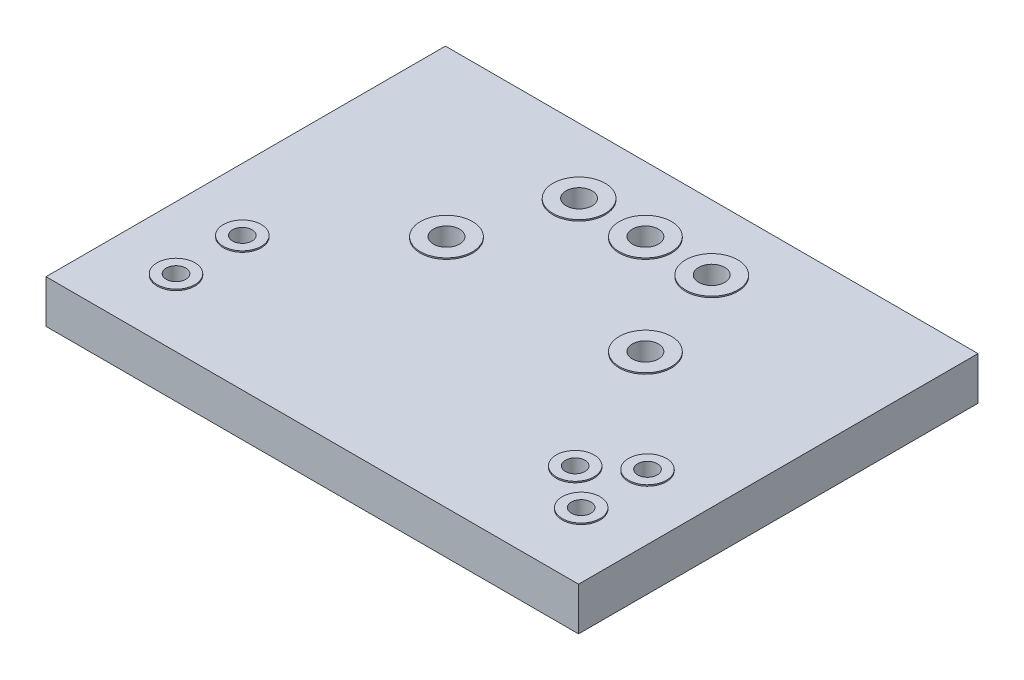
SolidWorks part; units mm, degrees
ref_plane "Front Plane" through (0, 0, 0) normal (0, 0, 1) x (1, 0, 0)
ref_plane "Top Plane" through (0, 0, 0) normal (0, 1, 0) x (1, 0, 0)
ref_plane "Right Plane" through (0, 0, 0) normal (1, 0, 0) x (0, 0, -1)
sketch "Sketch3" plane through (0, 0, 0) normal (0, 1, 0) x (1, 0, 0)
  line L0 (7.76, -2.57) -> (7.76, -5.11) construction
  line L1 (-10.2, 7.65) -> (10.2, 7.65)
  line L2 (-10.2, 7.65) -> (-10.2, -7.65)
  line L3 (-10.2, -7.65) -> (10.2, -7.65)
  line L4 (10.2, 7.65) -> (10.2, -7.65)
  line L5 (-10.2, 7.65) -> (10.2, -7.65) construction
  line L6 (-10.2, -7.65) -> (10.2, 7.65) construction
  line L7 (6.26, -3.84) -> (7.76, -3.84) construction
  line L8 (-7.76, -2.57) -> (-7.76, -5.11) construction
  line L9 (-7.76, -3.84) -> (7.76, -3.84) construction
  line L10 (-2.54, 5.11) -> (2.54, 5.11) construction
  line L11 (-3.81, 1.3) -> (3.81, 1.3) construction
  circle A0 centre (-2.54, 5.11) radius 0.5
  circle A1 centre (0, 5.11) radius 0.5
  circle A2 centre (2.54, 5.11) radius 0.5
  circle A3 centre (-7.76, -2.57) radius 0.375
  circle A4 centre (-7.76, -5.11) radius 0.375
  circle A5 centre (7.76, -2.57) radius 0.375
  circle A6 centre (7.76, -5.11) radius 0.375
  circle A7 centre (6.26, -3.84) radius 0.375
  circle A8 centre (-3.81, 1.3) radius 0.5
  circle A9 centre (3.81, 1.3) radius 0.5
  point P0 (0, 0)
  point P24 (0, -3.84)
  point P28 (0, 1.3)
  dimension "D5" = 0.75
  dimension "D7" = 1
  dimension "D1" = 15.3
  dimension "D2" = 20.4
  dimension "D3" = 1.5
  dimension "D4" = 2.54
  dimension "D6" = 15.52
  dimension "D8" = 2.54
  dimension "D9" = 2.54
  dimension "D10" = 2.54
  dimension "D11" = 7.62
  dimension "D12" = 3.81
extrude "Boss-Extrude2" add sketch "Sketch3" along normal mid plane 1.65
sketch "Sketch5" plane through (0, 0.825, 0) normal (0, 1, 0) x (1, 0, 0)
  circle A4 centre (7.76, -5.11) radius 0.375 construction
  circle A5 centre (6.26, -3.84) radius 0.375 construction
  circle A6 centre (7.76, -2.57) radius 0.375 construction
  circle A7 centre (-7.76, -5.11) radius 0.375 construction
  circle A8 centre (-7.76, -2.57) radius 0.375 construction
  circle A9 centre (-3.81, 1.3) radius 0.5 construction
  circle A10 centre (3.81, 1.3) radius 0.5 construction
  circle A11 centre (2.54, 5.11) radius 0.5 construction
  circle A12 centre (0, 5.11) radius 0.5 construction
  circle A13 centre (-2.54, 5.11) radius 0.5 construction
  circle A14 centre (7.76, -5.11) radius 0.375
  circle A15 centre (6.26, -3.84) radius 0.375
  circle A16 centre (7.76, -2.57) radius 0.375
  circle A17 centre (-7.76, -5.11) radius 0.375
  circle A18 centre (-7.76, -2.57) radius 0.375
  circle A19 centre (-3.81, 1.3) radius 0.5
  circle A20 centre (3.81, 1.3) radius 0.5
  circle A21 centre (2.54, 5.11) radius 0.5
  circle A22 centre (0, 5.11) radius 0.5
  circle A23 centre (-2.54, 5.11) radius 0.5
  circle A24 centre (-2.54, 5.11) radius 1
  circle A25 centre (0, 5.11) radius 1
  circle A26 centre (2.54, 5.11) radius 1
  circle A27 centre (3.81, 1.3) radius 1
  circle A28 centre (-3.81, 1.3) radius 1
  circle A29 centre (-7.76, -2.57) radius 0.725
  circle A30 centre (-7.76, -5.11) radius 0.725
  circle A31 centre (6.26, -3.84) radius 0.725
  circle A32 centre (7.76, -5.11) radius 0.725
  circle A33 centre (7.76, -2.57) radius 0.725
  dimension "D1" = 0.35
  dimension "D2" = 0.5
extrude "Boss-Extrude3" add sketch "Sketch5" along normal blind 0.05
mirror "Mirror1" about plane through (0, 0, 0) normal (0, 1, 0) of "Boss-Extrude3"
ref_point "Point1"
ref_plane "Plane2" through (0, 0, 5.11) normal (0, 0, 1) x (1, 0, 0)
sketch "Sketch6" plane through (0, -0.875, 0) normal (0, -1, 0) x (-1, 0, 0)
  point P0 (7.76, -2.57)
  point P1 (7.76, -5.11)
  point P3 (-7.76, -2.57)
  point P5 (-6.26, -3.84)
  point P7 (-7.76, -5.11)
  point P9 (0, 0)
